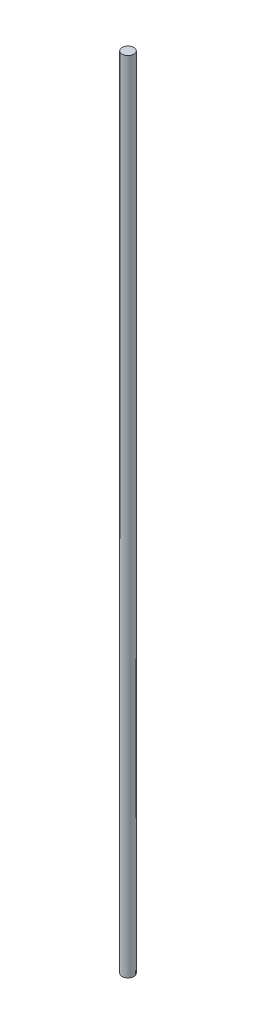
SolidWorks part; units mm, degrees
ref_plane "Front Plane" through (0, 0, 0) normal (0, 0, 1) x (1, 0, 0)
ref_plane "Top Plane" through (0, 0, 0) normal (0, 1, 0) x (1, 0, 0)
ref_plane "Right Plane" through (0, 0, 0) normal (1, 0, 0) x (0, 0, -1)
ref_plane "Plane1" through (0, 16.51, 0) normal (0, 1, 0) x (1, 0, 0)
sketch "Sketch6" plane through (0, 16.51, 0) normal (0, 1, 0) x (1, 0, 0)
  circle A1 centre (0, 0.6936) radius 0.3175
  dimension "D1" = 0.635
extrude "Boss-Extrude1" add sketch "Sketch6" along normal blind 43.18 separate body
